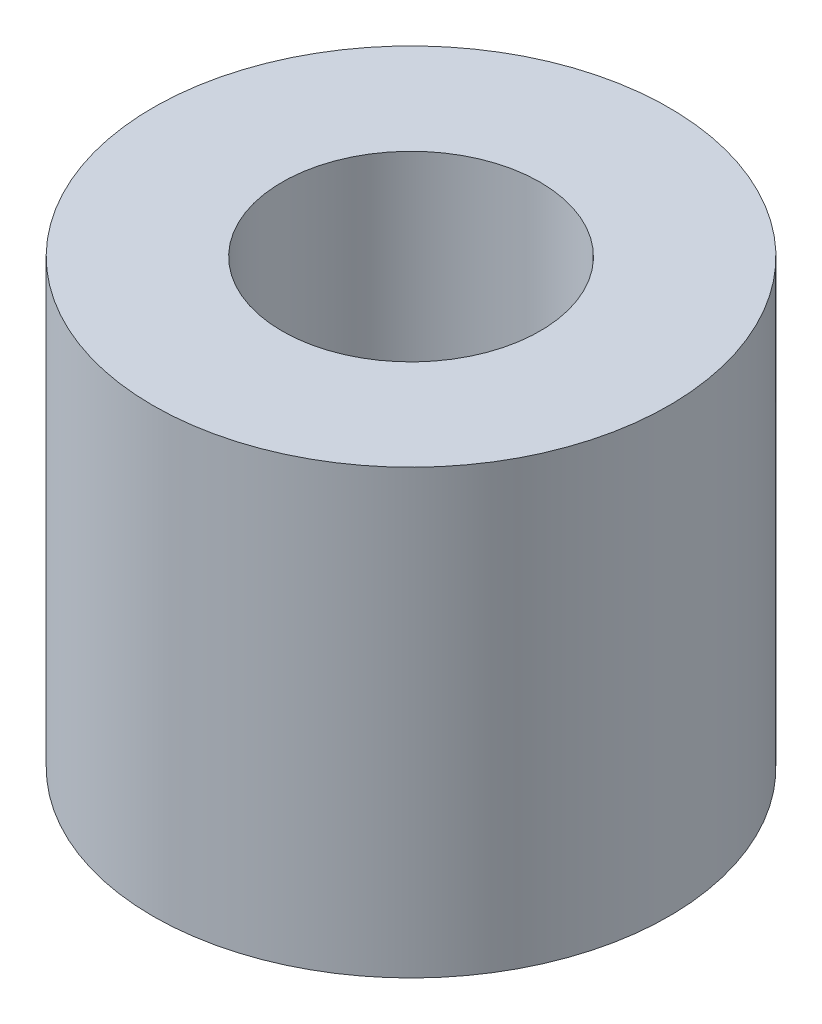
SolidWorks part; units mm, degrees
ref_plane "Front Plane" through (0, 0, 0) normal (0, 0, 1) x (1, 0, 0)
ref_plane "Top Plane" through (0, 0, 0) normal (0, 1, 0) x (1, 0, 0)
ref_plane "Right Plane" through (0, 0, 0) normal (1, 0, 0) x (0, 0, -1)
sketch "Sketch1" plane through (0, 0, 0) normal (0, 1, 0) x (1, 0, 0)
  circle A0 centre (0, 0) radius 3.5
  circle A1 centre (0, 0) radius 1.75
  dimension "D1" = 3.5
  dimension "D2" = 7
extrude "Boss-Extrude1" add sketch "Sketch1" along normal blind 6
